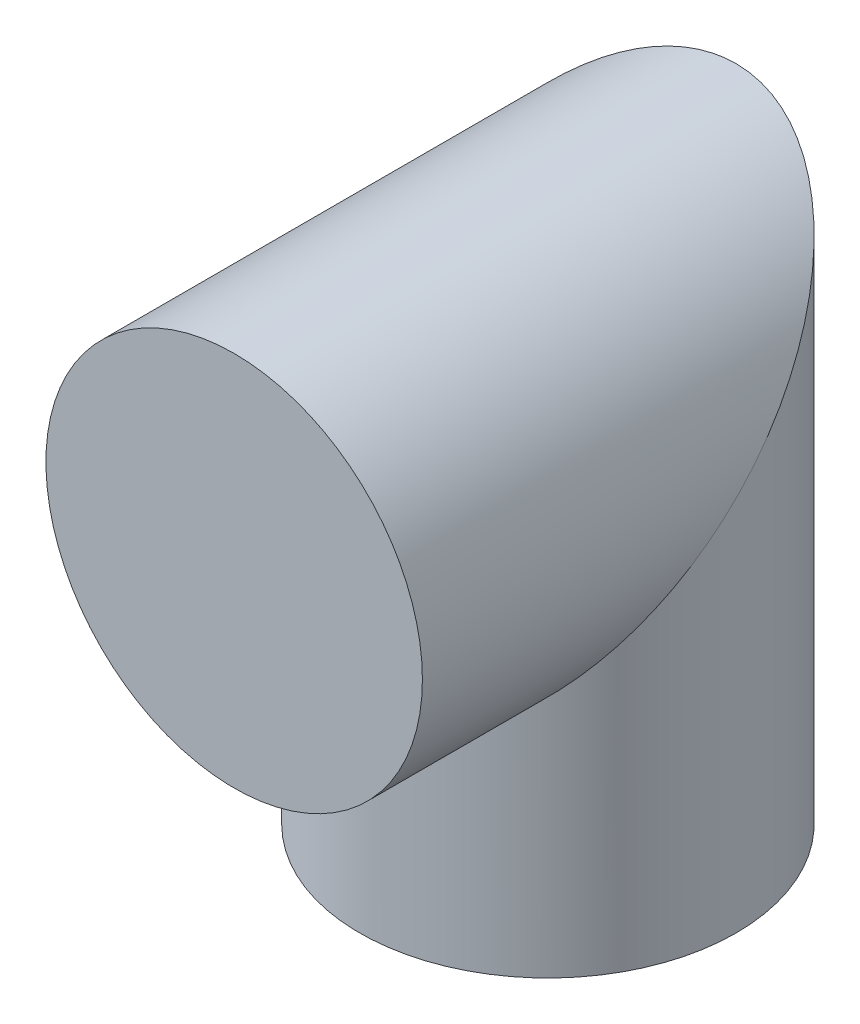
SolidWorks part; units mm, degrees
ref_plane "Front Plane" through (0, 0, 0) normal (0, 0, 1) x (1, 0, 0)
ref_plane "Top Plane" through (0, 0, 0) normal (0, 1, 0) x (1, 0, 0)
ref_plane "Right Plane" through (0, 0, 0) normal (1, 0, 0) x (0, 0, -1)
sketch "Sketch1" plane through (0, 0, 0) normal (1, 0, 0) x (0, 0, -1)
  line L0 (0, 0) -> (50, 0)
  line L1 (50, 0) -> (50, -60)
  point P2 (0, 0)
  dimension "D1" = 50
ref_plane "Plane1" through (0, 0, 0) normal (0, 0, 1) x (1, 0, 0)
sketch "Sketch3" plane through (0, 0, 0) normal (0, 0, 1) x (1, 0, 0)
  circle A0 centre (0, 0) radius 30
sweep "Sweep1" add profiles "Sketch3" path "Sketch1"
